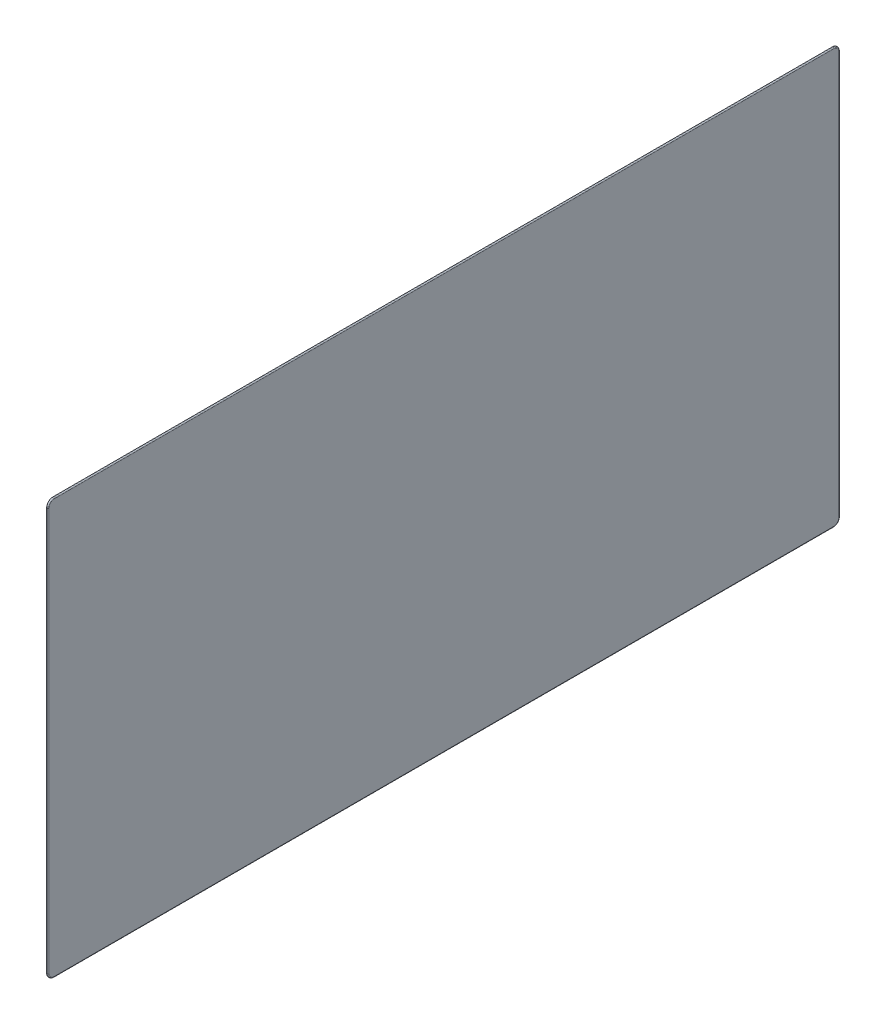
SolidWorks part; units mm, degrees
material "6061-T6 (SS)"
ref_plane "Front Plane" through (0, 0, 0) normal (0, 0, 1) x (1, 0, 0)
ref_plane "Top Plane" through (0, 0, 0) normal (0, 1, 0) x (1, 0, 0)
ref_plane "Right Plane" through (0, 0, 0) normal (1, 0, 0) x (0, 0, -1)
sketch "Sketch1" plane through (716.7, 0, 0) normal (1, 0, 0) x (0, 0, -1)
  line L18 (185.2189, 76) -> (185.2189, 264.432)
  line L19 (182.2189, 267.432) -> (0, 267.432)
  line L20 (0, 267.432) -> (-182.2189, 267.432)
  line L21 (-185.2189, 264.432) -> (-185.2189, 76)
  line L22 (-182.2189, 73) -> (0, 73)
  line L23 (0, 73) -> (182.2189, 73)
  line L24 (185.2189, 76) -> (185.2189, 264.432)
  line L25 (182.2189, 267.432) -> (0, 267.432)
  line L26 (0, 267.432) -> (-182.2189, 267.432)
  line L27 (-185.2189, 264.432) -> (-185.2189, 76)
  line L28 (-182.2189, 73) -> (0, 73)
  line L29 (0, 73) -> (182.2189, 73)
  arc A12 (185.2189, 264.432) -> (182.2189, 267.432) centre (182.2189, 264.432) ccw
  arc A13 (-182.2189, 267.432) -> (-185.2189, 264.432) centre (-182.2189, 264.432) ccw
  arc A14 (-185.2189, 76) -> (-182.2189, 73) centre (-182.2189, 76) ccw
  arc A15 (182.2189, 73) -> (185.2189, 76) centre (182.2189, 76) ccw
  arc A16 (185.2189, 264.432) -> (182.2189, 267.432) centre (182.2189, 264.432) ccw
  arc A17 (-182.2189, 267.432) -> (-185.2189, 264.432) centre (-182.2189, 264.432) ccw
  arc A18 (-185.2189, 76) -> (-182.2189, 73) centre (-182.2189, 76) ccw
  arc A19 (182.2189, 73) -> (185.2189, 76) centre (182.2189, 76) ccw
  dimension "D2" = 0
extrude "Boss-Extrude1" add sketch "Sketch1" along normal blind 0.61
fillet "Fillet1" radius 0.5 8 edges at (717.31, 73, 0) (717.31, 73.8787, 184.3402) (717.31, 170.216, 185.2189) (717.31, 266.5533, 184.3402) (717.31, 267.432, 0) (717.31, 266.5533, -184.3402) (717.31, 170.216, -185.2189) (717.31, 73.8787, -184.3402)
